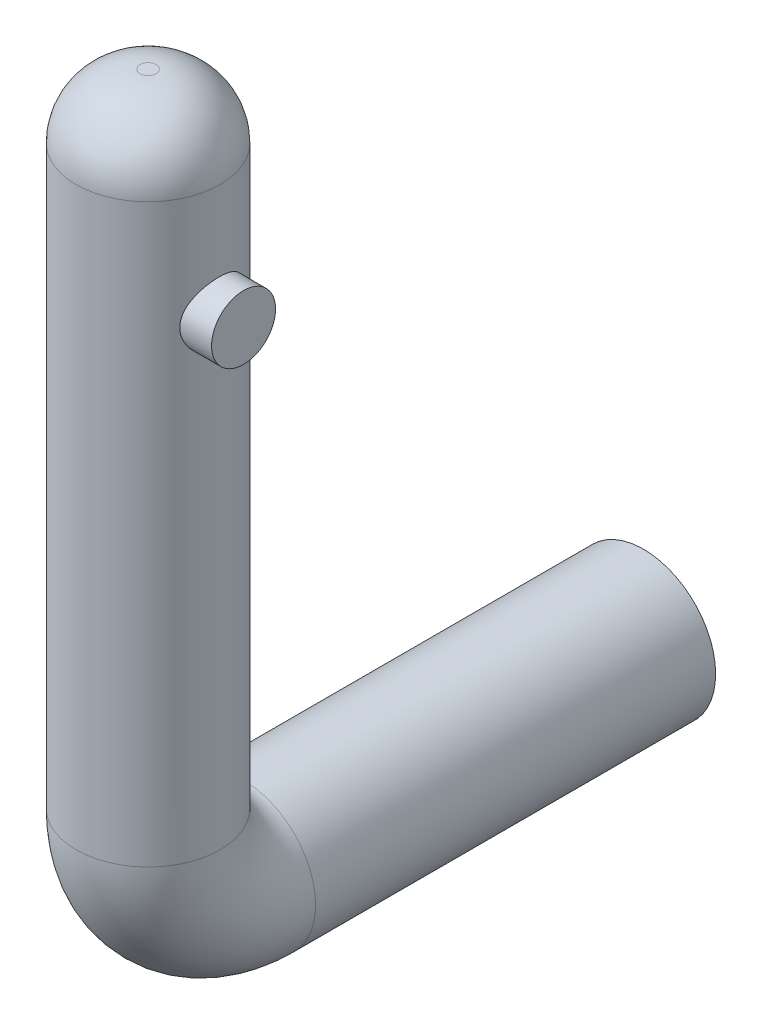
SolidWorks part; units mm, degrees
ref_plane "Front Plane" through (0, 0, 0) normal (0, 0, 1) x (1, 0, 0)
ref_plane "Top Plane" through (0, 0, 0) normal (0, 1, 0) x (1, 0, 0)
ref_plane "Right Plane" through (0, 0, 0) normal (1, 0, 0) x (0, 0, -1)
sketch "Sketch2" plane through (0, 0, 0) normal (0, 0, 1) x (1, 0, 0)
  circle A0 centre (0, 0) radius 4.5
  dimension "D1" = 9
sketch "Sketch3" plane through (0, 0, 0) normal (1, 0, 0) x (0, 0, -1)
  line L0 (0, 0) -> (-25, 0)
  line L1 (-30.9648, 5.9648) -> (-30.9648, 45.9648)
  arc A0 (-25, 0) -> (-30.9648, 5.9648) centre (-25, 5.9648) cw
  dimension "D3" = 5.9648
  dimension "D1" = 25
  dimension "D2" = 40
sweep "Sweep3" add profiles "Sketch2" path "Sketch3"
fillet "Fillet2" radius 4 1 edges at (4.5, 45.9648, 30.9648)
sketch "Sketch4" plane through (0, 0, 0) normal (1, 0, 0) x (0, 0, -1)
  circle A0 centre (-31, 35) radius 2
  dimension "D1" = 4
  dimension "D2" = 35
  dimension "D3" = 31
extrude "Boss-Extrude1" add sketch "Sketch4" along normal blind 6
